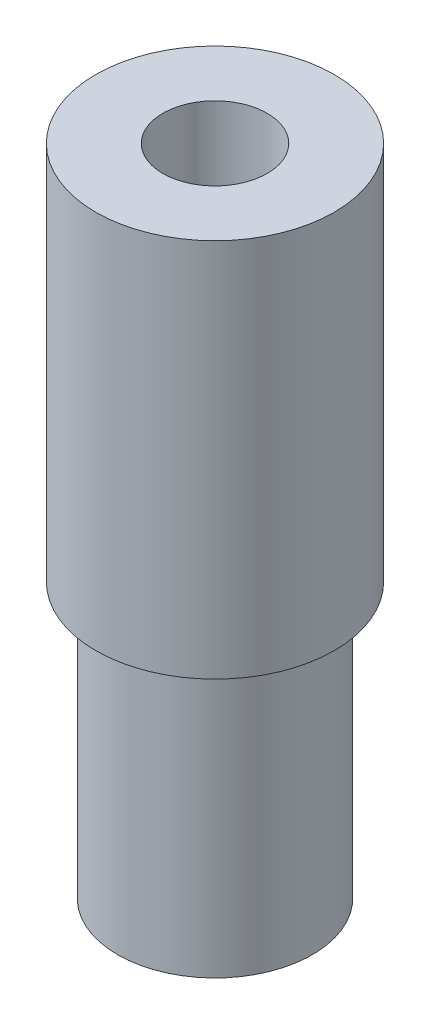
SolidWorks part; units mm, degrees
ref_plane "Front Plane" through (0, 0, 0) normal (0, 0, 1) x (1, 0, 0)
ref_plane "Top Plane" through (0, 0, 0) normal (0, 1, 0) x (1, 0, 0)
ref_plane "Right Plane" through (0, 0, 0) normal (1, 0, 0) x (0, 0, -1)
sketch "Sketch1" plane through (0, 0, 0) normal (0, 1, 0) x (1, 0, 0)
  circle A0 centre (0, 0) radius 4.9
  dimension "D1" = 9.8
extrude "Boss-Extrude1" add sketch "Sketch1" along normal blind 13.8
sketch "Sketch2" plane through (0, 13.8, 0) normal (0, 1, 0) x (1, 0, 0)
  circle A0 centre (0, 0) radius 6
  dimension "D1" = 12
extrude "Boss-Extrude2" add sketch "Sketch2" along normal blind 19.1
sketch "Sketch7" plane through (0, 0, 0) normal (0, 1, 0) x (1, 0, 0)
  circle A0 centre (0, 0) radius 2.625
  dimension "D1" = 5.25
extrude "Cut-Extrude1" cut sketch "Sketch7" along normal through all
chamfer "Chamfer1" distance 0.4 angle 45 1 edges at (0, 0, 2.625)
